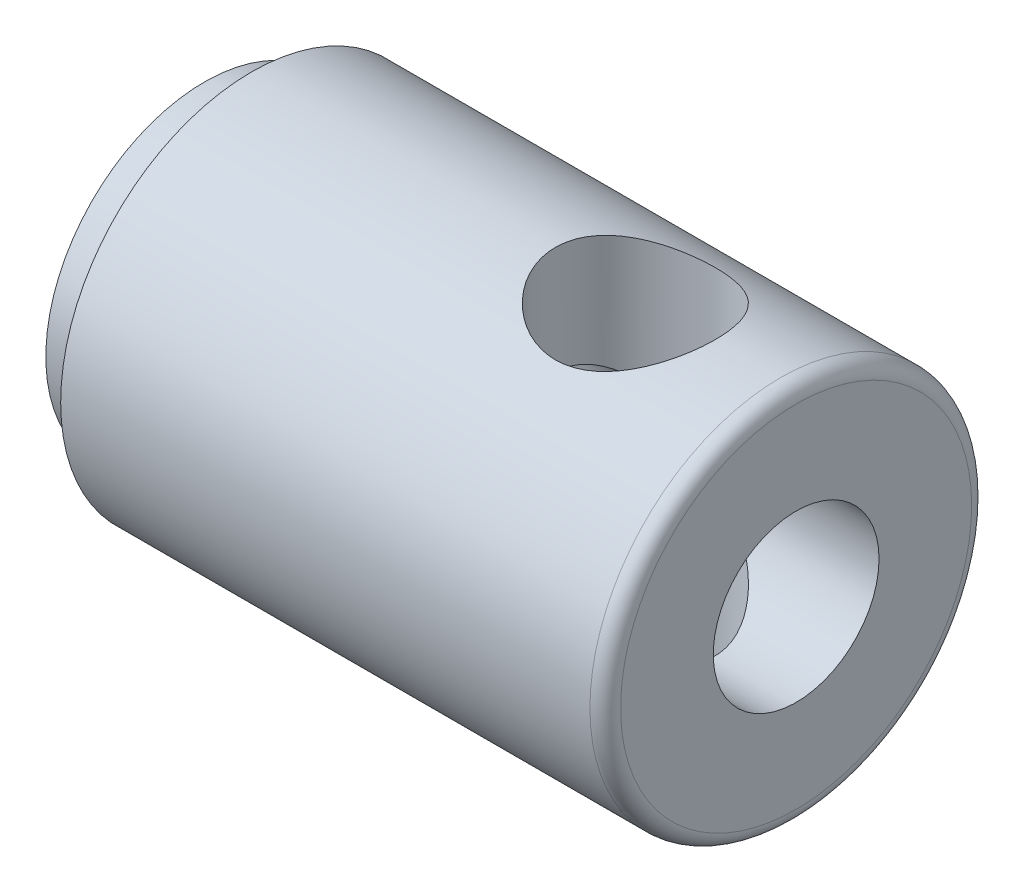
SolidWorks part; units mm, degrees
ref_plane "Front Plane" through (0, 0, 0) normal (0, 0, 1) x (1, 0, 0)
ref_plane "Top Plane" through (0, 0, 0) normal (0, 1, 0) x (1, 0, 0)
ref_plane "Right Plane" through (0, 0, 0) normal (1, 0, 0) x (0, 0, -1)
sketch "Sketch1" plane through (0, 0, 0) normal (0, 0, 1) x (1, 0, 0)
  line L0 (0, 0) -> (-50000, 0) construction
  line L1 (0, 2.0574) -> (-12.9318, 2.0574)
  line L3 (-14.6844, 3.937) -> (-13.516, 3.937)
  line L4 (-13.516, 3.937) -> (-13.516, 4.7371)
  line L5 (-13.516, 4.7371) -> (-0.381, 4.7371)
  line L6 (0, 4.3561) -> (0, 2.0574)
  line L7 (-14.6844, 3.937) -> (-14.6844, 3.81)
  line L8 (-14.6844, 3.81) -> (-12.9318, 2.0574)
  arc A0 (0, 4.3561) -> (-0.381, 4.7371) centre (-0.381, 4.3561) ccw
  point P11 (-52.0626, 2.0574)
  point P13 (-2.3928, 2.0574)
  dimension "D1" = 0.381
  dimension "D2" = 7.874
  dimension "D3" = 7.62
  dimension "D4" = 4.1148
  dimension "D5" = 14.6844
  dimension "D6" = 1.1684
  dimension "D7" = 9.4742
  dimension "D8" = 45
revolve "Revolve1" add sketch "Sketch1" angle 360 about L0
sketch "Sketch2" plane through (0, 0, 0) normal (0, 1, 0) x (1, 0, 0)
  line L0 (-13.516, 3.937) -> (-13.516, -3.937) construction
  circle A0 centre (-3.991, 0) radius 1.9844
  point P4 (-3.991, -0.1776)
  dimension "D2" = 3.9688
  dimension "D1" = 9.525
extrude "Cut-Extrude1" cut sketch "Sketch2" against normal through all both and the other way through all contours A0
